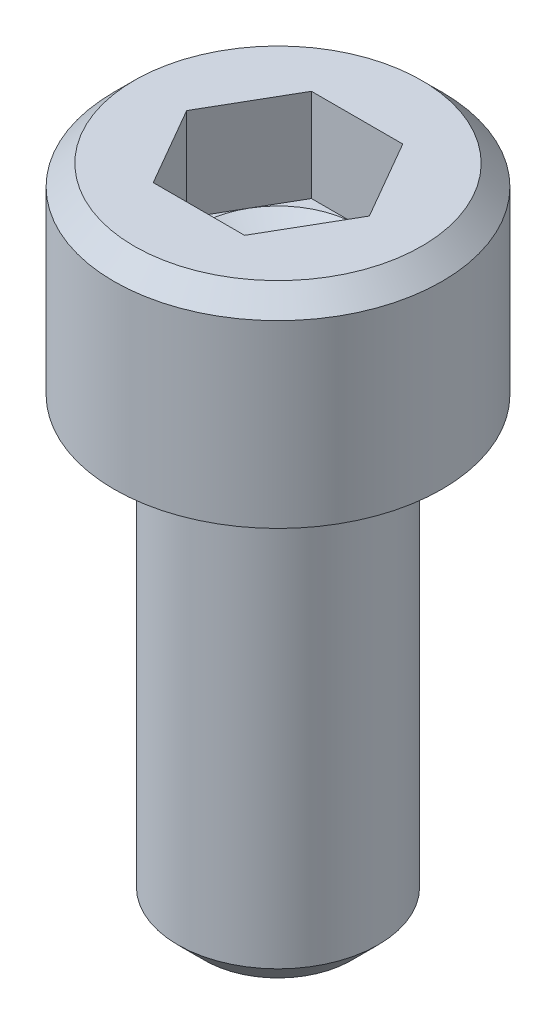
SolidWorks part; units mm, degrees
material "Alloy Steel"
ref_plane "Front Plane" through (0, 0, 0) normal (0, 0, 1) x (1, 0, 0)
ref_plane "Top Plane" through (0, 0, 0) normal (0, 1, 0) x (1, 0, 0)
ref_plane "Right Plane" through (0, 0, 0) normal (1, 0, 0) x (0, 0, -1)
sketch "Sketch1" plane through (0, 0, 0) normal (0, 0, 1) x (1, 0, 0)
  line L0 (2.8702, 3.5052) -> (0, 3.5052)
  line L1 (0, 3.5052) -> (0, 0)
  line L2 (0, 0) -> (2.8702, 0)
  line L3 (2.8702, 0) -> (2.8702, 3.5052)
  line L4 (0, 3.5052) -> (0, 0) construction
revolve "Revolve1" add sketch "Sketch1" angle 360 about L4
sketch "Sketch2" plane through (0, 0, 0) normal (0, -1, 0) x (1, 0, 0)
  circle A0 centre (0, 0) radius 1.7526
extrude "Boss-Extrude1" add sketch "Sketch2" along normal blind 7.9375
sketch "Sketch3" plane through (0, 3.5052, 0) normal (0, 1, 0) x (-1, 0, 0)
  line L0 (-0.7992, 1.3843) -> (-1.5985, 0)
  line L1 (-1.5985, 0) -> (-0.7992, -1.3843)
  line L2 (-0.7992, -1.3843) -> (0.7992, -1.3843)
  line L3 (0.7992, -1.3843) -> (1.5985, 0)
  line L4 (1.5985, 0) -> (0.7992, 1.3843)
  line L5 (0.7992, 1.3843) -> (-0.7992, 1.3843)
extrude "Cut-Extrude1" cut sketch "Sketch3" against normal blind 1.6256
sketch "Sketch4" plane through (0, 0, 0) normal (0, 0, 1) x (1, 0, 0)
  line L0 (1.3843, 1.8796) -> (0, 1.8796)
  line L1 (0, 1.8796) -> (0, 1.0804)
  line L2 (0, 1.0804) -> (1.3843, 1.8796)
  line L3 (0, 1.8796) -> (0, 1.0803) construction
revolve "Cut-Revolve1" cut sketch "Sketch4" angle 360 about L3
chamfer "Chamfer1" distance 0.4724 angle 45 1 edges at (0, -7.9375, -1.7526)
chamfer "Chamfer2" distance 0.3556 angle 45 1 edges at (0, 3.5052, -2.8702)
fillet "Fillet1" radius 0.254 1 edges at (0, 0, -1.7526)
